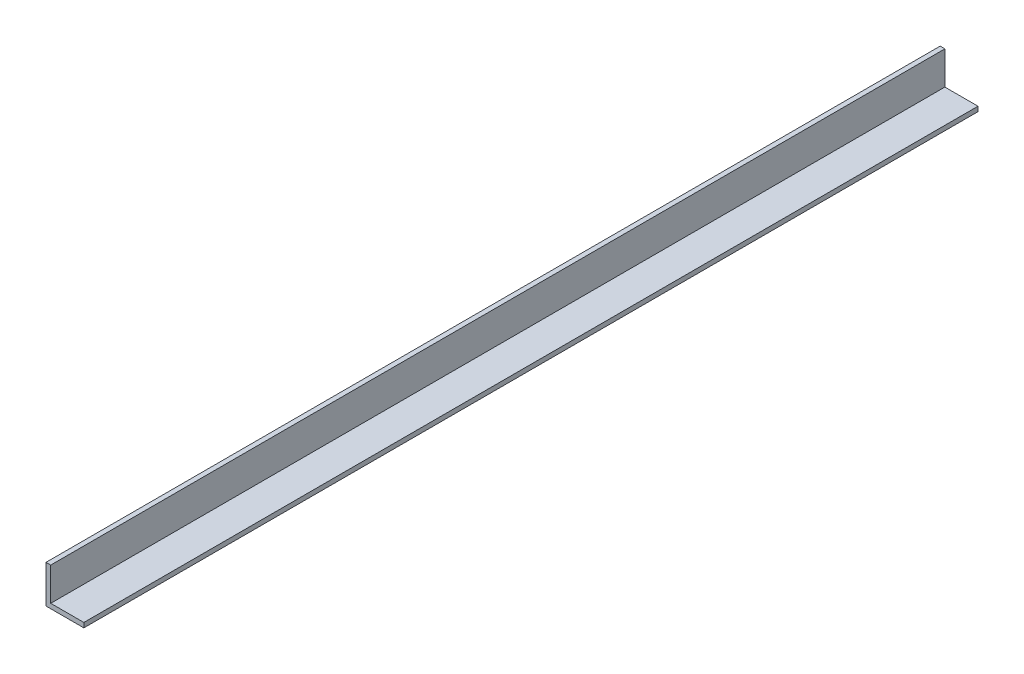
SolidWorks part; units mm, degrees
ref_plane "Front Plane" through (0, 0, 0) normal (0, 0, 1) x (1, 0, 0)
ref_plane "Top Plane" through (0, 0, 0) normal (0, 1, 0) x (1, 0, 0)
ref_plane "Right Plane" through (0, 0, 0) normal (1, 0, 0) x (0, 0, -1)
sketch "Sketch1" plane through (0, 0, 0) normal (0, 0, 1) x (1, 0, 0)
  line L0 (0, 25.4) -> (0, 0) construction
  line L1 (0, 0) -> (25.4, 0) construction
  line L2 (25.4, 0) -> (25.4, 3.175) construction
  line L3 (25.4, 3.175) -> (3.175, 3.175) construction
  line L4 (3.175, 3.175) -> (3.175, 25.4) construction
  line L6 (3.175, 25.4) -> (0, 25.4) construction
  arc A0 (3.175, 3.5814) -> (3.5814, 3.175) centre (3.5814, 3.5814) ccw construction
  point P4 (0, 0)
  dimension "Inside Corner Radius" = 0.4064
  dimension "Outside Height" = 25.4
  dimension "Inside Height" = 22.225
  dimension "Outside Width" = 25.4
  dimension "Inside Width" = 22.225
  dimension "Wall Thickness" = 3.175
  dimension "Shape" = 90
sketch "Sketch2" plane through (0, 0, 0) normal (1, 0, 0) x (0, 0, -1)
  line L0 (1219.2, 0) -> (-1219.2, 0) construction
  line L1 (-1219.2, 25.4) -> (-1219.2, 0) construction
  line L2 (1219.2, 25.4) -> (1219.2, 0) construction
  point P0 (-1189.99, 0)
  point P4 (0, 0)
  point P6 (1189.99, 0)
  dimension "D1" = 29.21
  dimension "D2" = 29.21
  dimension "D3" = 25.4
  dimension "Length" = 2438.4
sketch "Sketch3" plane through (0, 0, 0) normal (0, 0, 1) x (1, 0, 0)
  line L0 (3.175, 25.4) -> (0, 25.4)
  line L1 (0, 25.4) -> (0, 0)
  line L2 (0, 0) -> (25.4, 0)
  line L3 (25.4, 0) -> (25.4, 3.175)
  line L4 (25.4, 3.175) -> (3.175, 3.175)
  line L5 (3.175, 3.175) -> (3.175, 25.4)
extrude "Boss-Extrude1" add sketch "Sketch3" along normal mid plane 2438.4
fillet "Fillet1" radius 0.4064 1 edges at (3.175, 3.175, 0)
sketch "Sketch4" plane through (0, 0, 0) normal (-1, 0, 0) x (0, 0, 1)
  line L0 (1219.2, 25.4) -> (1219.2, 0) construction
  line L1 (-1219.2, 25.4) -> (619.2, 25.4)
  line L2 (-1219.2, 25.4) -> (-1219.2, -77.8785)
  line L3 (-1219.2, -77.8785) -> (619.2, -77.8785)
  line L4 (619.2, 25.4) -> (619.2, -77.8785)
  dimension "D1" = 600
extrude "Cut-Extrude1" cut sketch "Sketch4" against normal blind 60
sketch "Sketch5" plane through (0, 0, 619.2) normal (0, 0, -1) x (-1, 0, 0)
  line L0 (-3.175, 3.5814) -> (-3.175, 25.4) construction
  line L1 (-3.175, 5.146) -> (-6.0134, 5.146)
  line L2 (-3.175, 5.146) -> (-3.175, 3.175)
  line L3 (-3.175, 3.175) -> (-6.0134, 3.175)
  line L4 (-6.0134, 5.146) -> (-6.0134, 3.175)
  line L5 (-25.4, 3.175) -> (-3.5814, 3.175) construction
extrude "Cut-Extrude2" cut sketch "Sketch5" against normal blind 700
equation "\"D1@Boss-Extrude1\"=\"Length@Sketch2\""
equation "\"D1@Sketch2\" = \"Outside Width@Sketch1\" * 1.15"
equation "\"D2@Sketch2\"=\"D1@Sketch2\""
equation "\"D1@Fillet1\"=\"Inside Corner Radius@Sketch1\""
equation "\"D3@Sketch2\"=\"Outside Height@Sketch1\""
